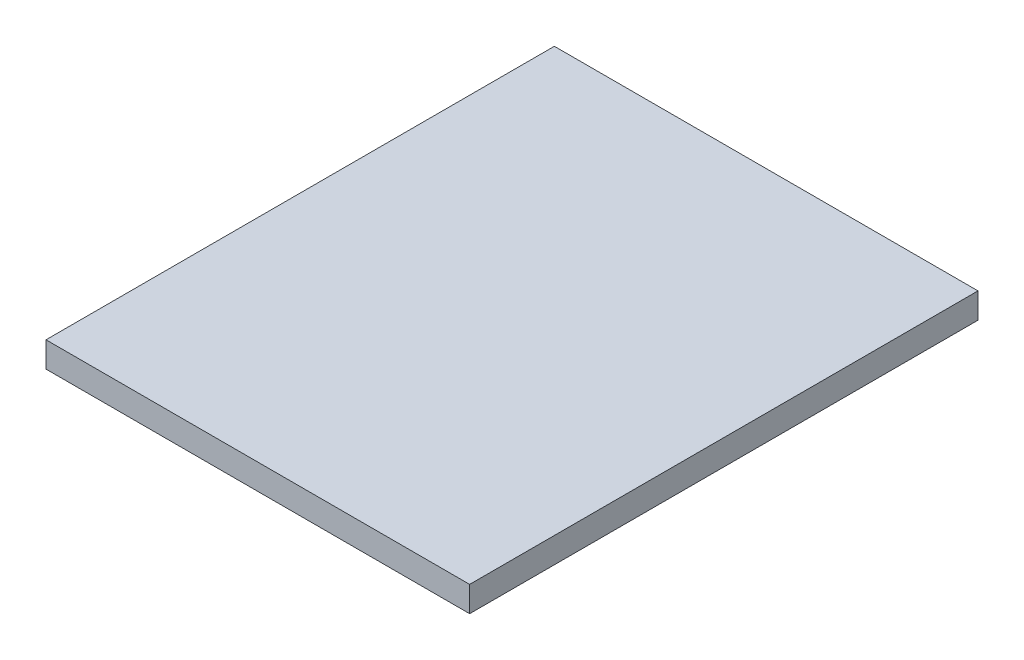
SolidWorks part; units mm, degrees
ref_plane "Front Plane" through (0, 0, 0) normal (0, 0, 1) x (1, 0, 0)
ref_plane "Top Plane" through (0, 0, 0) normal (0, 1, 0) x (1, 0, 0)
ref_plane "Right Plane" through (0, 0, 0) normal (1, 0, 0) x (0, 0, -1)
sketch "Sketch1" plane through (0, 0, 0) normal (0, 1, 0) x (1, 0, 0)
  line L1 (-90.8046, 75.5747) -> (9.1954, 75.5747)
  line L2 (-90.8046, 75.5747) -> (-90.8046, -44.4253)
  line L3 (-90.8046, -44.4253) -> (9.1954, -44.4253)
  line L4 (9.1954, 75.5747) -> (9.1954, -44.4253)
  dimension "D1" = 120
  dimension "D2" = 100
extrude "Boss-Extrude1" add sketch "Sketch1" along normal blind 6
